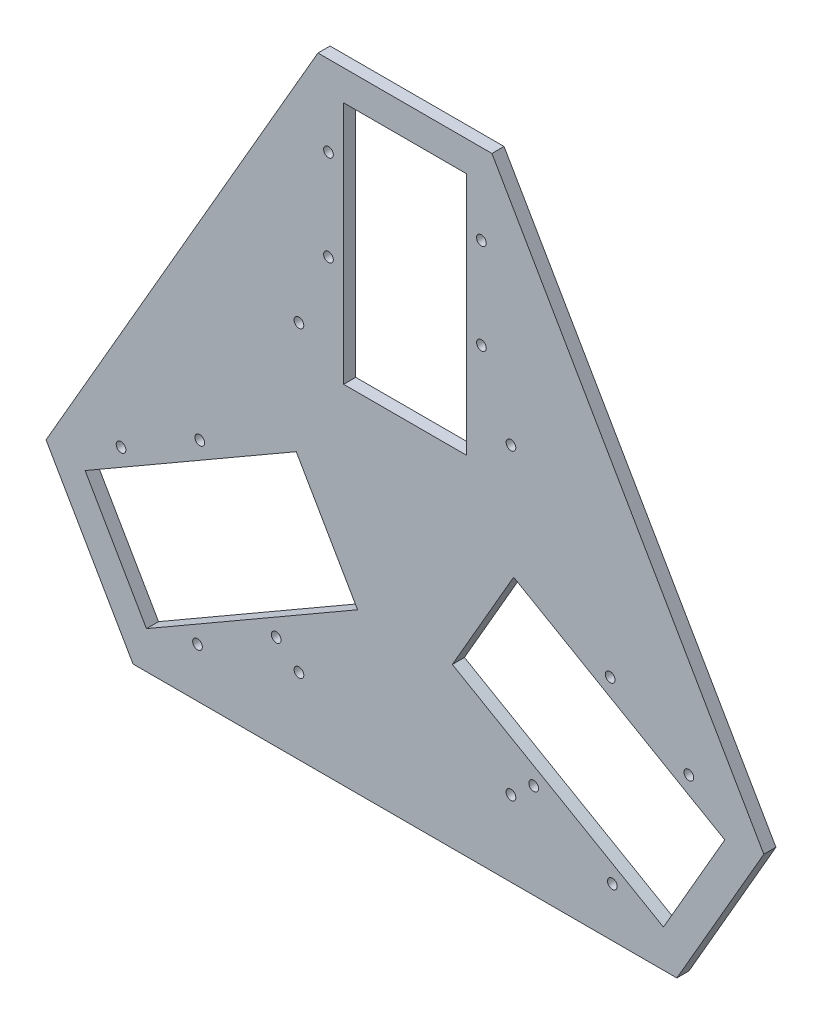
SolidWorks part; units mm, degrees
ref_plane "正面" through (0, 0, 0) normal (0, 0, 1) x (1, 0, 0)
ref_plane "平面" through (0, 0, 0) normal (0, 1, 0) x (1, 0, 0)
ref_plane "右側面" through (0, 0, 0) normal (1, 0, 0) x (0, 0, -1)
sketch "ｽｹｯﾁ1" plane through (0, 0, 0) normal (0, 0, 1) x (1, 0, 0)
  line L0 (0, -55) -> (0, 55) construction
  line L1 (-20.25, 110.25) -> (20.25, 110.25)
  line L2 (-20.25, 110.25) -> (-20.25, 29.75)
  line L3 (-20.25, 29.75) -> (20.25, 29.75)
  line L4 (20.25, 110.25) -> (20.25, 29.75)
  line L5 (-20.25, 110.25) -> (20.25, 29.75) construction
  line L6 (-20.25, 29.75) -> (20.25, 110.25) construction
  line L7 (0, 70) -> (0, 0) construction
  line L9 (25.25, 93.6603) -> (25.25, 63.6603) construction
  line L10 (-25.25, 93.6603) -> (-25.25, 63.6603) construction
  line L11 (105.6043, -37.588) -> (85.3543, -72.662)
  line L12 (105.6043, -37.588) -> (35.8893, 2.662)
  line L13 (85.3543, -72.662) -> (15.6393, -32.412)
  line L14 (35.8893, 2.662) -> (15.6393, -32.412)
  line L15 (105.6043, -37.588) -> (15.6393, -32.412) construction
  line L16 (35.8893, 2.662) -> (85.3543, -72.662) construction
  line L17 (60.6218, -35) -> (0, 0) construction
  line L18 (93.7372, -24.963) -> (67.7564, -9.963) construction
  line L19 (68.4872, -68.6973) -> (42.5064, -53.6973) construction
  line L20 (-85.3543, -72.662) -> (-105.6043, -37.588)
  line L21 (-85.3543, -72.662) -> (-15.6393, -32.412)
  line L22 (-105.6043, -37.588) -> (-35.8893, 2.662)
  line L23 (-15.6393, -32.412) -> (-35.8893, 2.662)
  line L24 (-85.3543, -72.662) -> (-35.8893, 2.662) construction
  line L25 (-15.6393, -32.412) -> (-105.6043, -37.588) construction
  line L26 (-60.6218, -35) -> (0, 0) construction
  line L27 (-68.4872, -68.6973) -> (-42.5064, -53.6973) construction
  line L28 (-93.7372, -24.963) -> (-67.7564, -9.963) construction
  line L29 (55, 0) -> (-55, 0) construction
  line L30 (-28.7232, 120.25) -> (28.7232, 120.25)
  line L31 (0, 170) -> (-147.2243, -85) construction
  line L32 (-147.2243, -85) -> (147.2243, -85) construction
  line L33 (147.2243, -85) -> (0, 170) construction
  line L34 (28.7232, 120.25) -> (118.5011, -35.25)
  line L35 (118.5011, -35.25) -> (89.778, -85)
  line L36 (89.778, -85) -> (-89.778, -85)
  line L37 (-89.778, -85) -> (-118.5011, -35.25)
  line L38 (-118.5011, -35.25) -> (-28.7232, 120.25)
  line L40 (-35, -60) -> (35, -60) construction
  line L41 (-35, -60) -> (-35, 40) construction
  line L42 (-35, 40) -> (35, 40) construction
  line L43 (35, -60) -> (35, 40) construction
  line L44 (-35, -60) -> (35, 40) construction
  line L45 (-35, 40) -> (35, -60) construction
  circle A0 centre (25.25, 93.6603) radius 1.6
  circle A1 centre (25.25, 63.6603) radius 1.6
  circle A2 centre (-25.25, 63.6603) radius 1.6
  circle A3 centre (-25.25, 93.6603) radius 1.6
  circle A4 centre (68.4872, -68.6973) radius 1.6
  circle A5 centre (93.7372, -24.963) radius 1.6
  circle A6 centre (67.7564, -9.963) radius 1.6
  circle A7 centre (42.5064, -53.6973) radius 1.6
  circle A8 centre (-93.7372, -24.963) radius 1.6
  circle A9 centre (-68.4872, -68.6973) radius 1.6
  circle A10 centre (-42.5064, -53.6973) radius 1.6
  circle A11 centre (-67.7564, -9.963) radius 1.6
  circle A12 centre (0, 0) radius 85 construction
  circle A13 centre (-35, 40) radius 1.6
  circle A14 centre (35, 40) radius 1.6
  circle A15 centre (35, -60) radius 1.6
  circle A16 centre (-35, -60) radius 1.6
  point P0 (0, 70)
  point P19 (25.25, 78.6603)
  point P46 (0, 0)
  point P48 (0, -85)
  point P59 (0, -10)
  dimension "D1" = 3.2
  dimension "D12" = 3.2
  dimension "D2" = 40.5
  dimension "D3" = 80.5
  dimension "D4" = 30
  dimension "D5" = 5
  dimension "D6" = 70
  dimension "D8" = 78.6603
  dimension "D9" = 85
  dimension "D10" = 10
  dimension "D11" = 10
  dimension "D13" = 100
  dimension "D14" = 70
  dimension "D7" = 3
extrude "ﾎﾞｽ - 押し出し1" add sketch "ｽｹｯﾁ1" along normal blind 4
equation "\"D3@ｽｹｯﾁ1\"=40/sin(30)+0.5"
equation "\"D8@ｽｹｯﾁ1\"=70+5/tan(30)"
